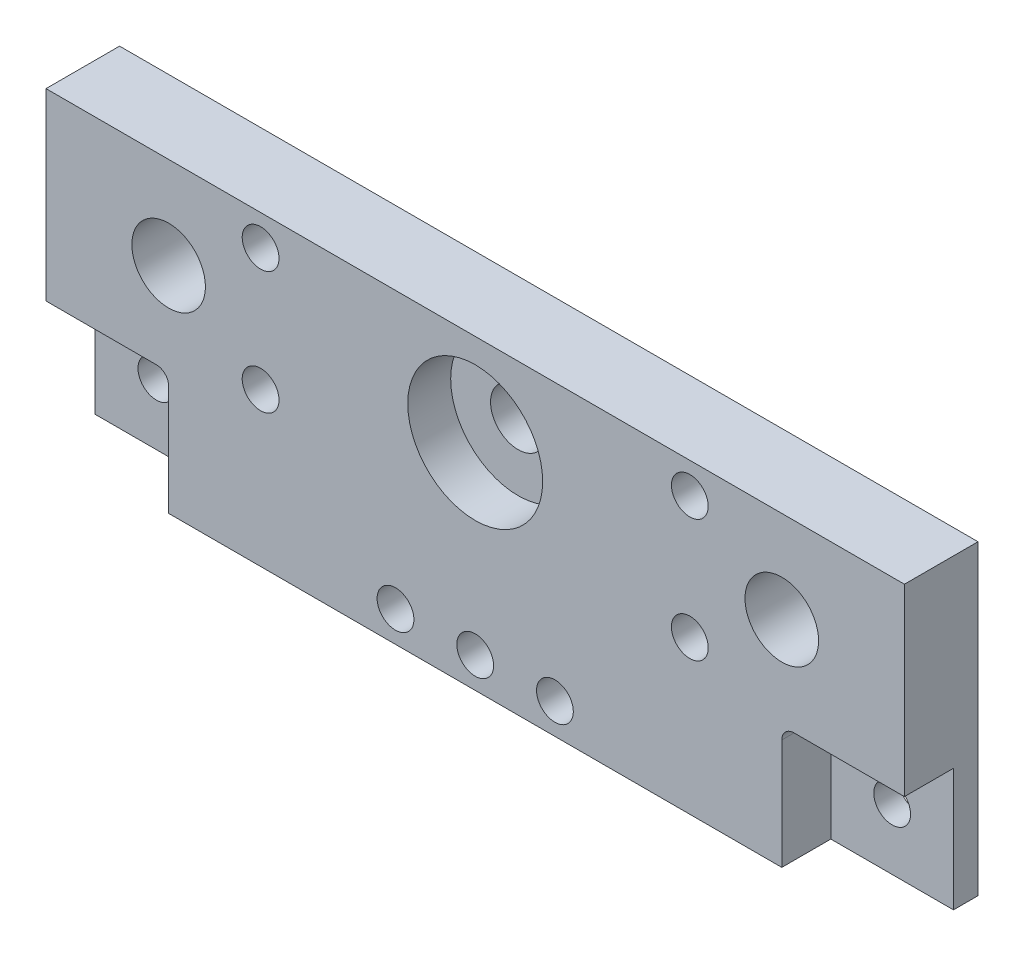
SolidWorks part; units mm, degrees
ref_plane "Plan de face" through (0, 0, 0) normal (0, 0, 1) x (1, 0, 0)
ref_plane "Plan de dessus" through (0, 0, 0) normal (0, 1, 0) x (1, 0, 0)
ref_plane "Plan de droite" through (0, 0, 0) normal (1, 0, 0) x (0, 0, -1)
sketch "Esquisse1" plane through (0, 0, 0) normal (0, 0, 1) x (1, 0, 0)
  line L0 (49.9563, -13.0813) -> (49.9563, -43.0813) construction
  line L1 (-20.0437, -13.0813) -> (119.9563, -13.0813)
  line L2 (-20.0437, -13.0813) -> (-20.0437, -43.0813)
  line L3 (-20.0437, -43.0813) -> (119.9563, -43.0813)
  line L4 (119.9563, -13.0813) -> (119.9563, -43.0813)
  line L5 (-20.0437, -28.0813) -> (119.9563, -28.0813) construction
  line L6 (14.9563, -13.0813) -> (14.9563, -43.0813) construction
  line L7 (84.9563, -13.0813) -> (84.9563, -43.0813) construction
  circle A0 centre (49.9563, -28.0813) radius 11
  circle A1 centre (-0.0437, -28.0813) radius 6
  circle A2 centre (99.9563, -28.0813) radius 6
  circle A4 centre (14.9563, -18.0813) radius 3
  circle A5 centre (14.9563, -38.0813) radius 3
  circle A7 centre (84.9563, -18.0813) radius 3
  circle A8 centre (84.9563, -38.0813) radius 3
  dimension "D3" = 22
  dimension "D4" = 12
  dimension "D5" = 12
  dimension "D9" = 35
  dimension "D10" = 35
  dimension "D12" = 6
  dimension "D13" = 6
  dimension "D16" = 6
  dimension "D17" = 6
  dimension "D1" = 30
  dimension "D2" = 140
  dimension "D6" = 100
  dimension "D7" = 50
  dimension "D18" = 20
  dimension "D19" = 10
  dimension "D20" = 20
  dimension "D21" = 10
extrude "Extrusion1" add sketch "Esquisse1" along normal blind 8
sketch "Esquisse2" plane through (0, 0, 0) normal (0, 0, -1) x (-1, 0, 0)
  line L1 (-119.9563, -13.0813) -> (20.0437, -13.0813)
  line L2 (-119.9563, -13.0813) -> (-119.9563, -63.0813)
  line L3 (-119.9563, -63.0813) -> (20.0437, -63.0813)
  line L4 (20.0437, -13.0813) -> (20.0437, -63.0813)
  dimension "D1" = 140
  dimension "D2" = 50
extrude "Boss.-Extru.1" add sketch "Esquisse2" along normal blind 4
sketch "Esquisse3" plane through (0, 0, 0) normal (0, 0, 1) x (1, 0, 0)
  line L0 (-20.0437, -53.0813) -> (119.9563, -53.0813) construction
  line L1 (-20.0437, -63.0813) -> (-20.0437, -43.0813) construction
  line L2 (119.9563, -43.0813) -> (119.9563, -63.0813) construction
  circle A0 centre (-10.0437, -53.0813) radius 3
  circle A1 centre (109.9563, -53.0813) radius 3
  dimension "D1" = 6
  dimension "D2" = 6
  dimension "D4" = 10
  dimension "D3" = 10
extrude "Enlèv. mat.-Extru.1" cut sketch "Esquisse3" against normal through all
sketch "Esquisse4" plane through (0, 0, 0) normal (0, 0, 1) x (1, 0, 0)
  circle A0 centre (49.9563, -28.0813) radius 11
  circle A1 centre (14.9563, -18.0813) radius 3
  circle A2 centre (14.9563, -38.0813) radius 3
  circle A3 centre (84.9563, -18.0813) radius 3
  circle A4 centre (84.9563, -38.0813) radius 3
extrude "Enlèv. mat.-Extru.2" cut sketch "Esquisse4" against normal through all
sketch "Esquisse5" plane through (0, 0, 0) normal (0, 0, 1) x (1, 0, 0)
  line L0 (-20.0437, -43.0813) -> (119.9563, -43.0813) construction
  line L1 (-0.0437, -43.0813) -> (99.9563, -43.0813)
  line L2 (-0.0437, -43.0813) -> (-0.0437, -63.0813)
  line L3 (-0.0437, -63.0813) -> (99.9563, -63.0813)
  line L4 (99.9563, -43.0813) -> (99.9563, -63.0813)
  line L5 (119.9563, -63.0813) -> (-20.0437, -63.0813) construction
  line L6 (-20.0437, -63.0813) -> (-20.0437, -43.0813) construction
  line L7 (119.9563, -43.0813) -> (119.9563, -63.0813) construction
  dimension "D1" = 20
  dimension "D2" = 20
extrude "Boss.-Extru.2" add sketch "Esquisse5" along normal blind 8
sketch "Esquisse6" plane through (0, 0, 8) normal (0, 0, 1) x (1, 0, 0)
  line L0 (-0.0437, -58.0813) -> (99.9563, -58.0813) construction
  line L1 (-0.0437, -43.0813) -> (-0.0437, -63.0813) construction
  line L2 (99.9563, -63.0813) -> (99.9563, -43.0813) construction
  line L3 (-0.0437, -63.0813) -> (99.9563, -63.0813) construction
  line L4 (49.9563, -13.0813) -> (49.9563, -63.0813) construction
  line L5 (119.9563, -13.0813) -> (-20.0437, -13.0813) construction
  circle A0 centre (62.9563, -58.0813) radius 3
  circle A1 centre (36.9563, -58.0813) radius 3
  dimension "D2" = 6
  dimension "D3" = 6
  dimension "D1" = 5
  dimension "D4" = 26
  dimension "D5" = 13
extrude "Enlèv. mat.-Extru.3" cut sketch "Esquisse6" against normal blind 8
sketch "Esquisse7" plane through (0, 0, -4) normal (0, 0, -1) x (-1, 0, 0)
  circle A0 centre (-49.9563, -28.0813) radius 11
extrude "Boss.-Extru.3" add sketch "Esquisse7" against normal blind 5
sketch "Esquisse8" plane through (0, 0, 1) normal (0, 0, 1) x (1, 0, 0)
  circle A0 centre (49.9563, -28.0813) radius 4.5
  dimension "D1" = 9
extrude "Enlèv. mat.-Extru.4" cut sketch "Esquisse8" against normal through all
sketch "Esquisse9" plane through (0, 0, 0) normal (0, 0, 1) x (1, 0, 0)
  circle A0 centre (-0.0437, -28.0813) radius 6
  circle A1 centre (99.9563, -28.0813) radius 6
extrude "Enlèv. mat.-Extru.5" cut sketch "Esquisse9" against normal blind 2
sketch "Esquisse10" plane through (0, 0, 8) normal (0, 0, 1) x (1, 0, 0)
  line L0 (-0.0437, -63.0813) -> (99.9563, -63.0813) construction
  line L1 (-20.0437, -63.0813) -> (-20.0437, -43.0813) construction
  circle A0 centre (49.9563, -58.0813) radius 3
  dimension "D1" = 6
  dimension "D2" = 5
  dimension "D3" = 70
extrude "Enlèv. mat.-Extru.6" cut sketch "Esquisse10" against normal through all
fillet "Congé1" radius 2 1 edges at (-0.0437, -43.0813, 4)
fillet "Congé2" radius 2 1 edges at (99.9563, -43.0813, 4)
